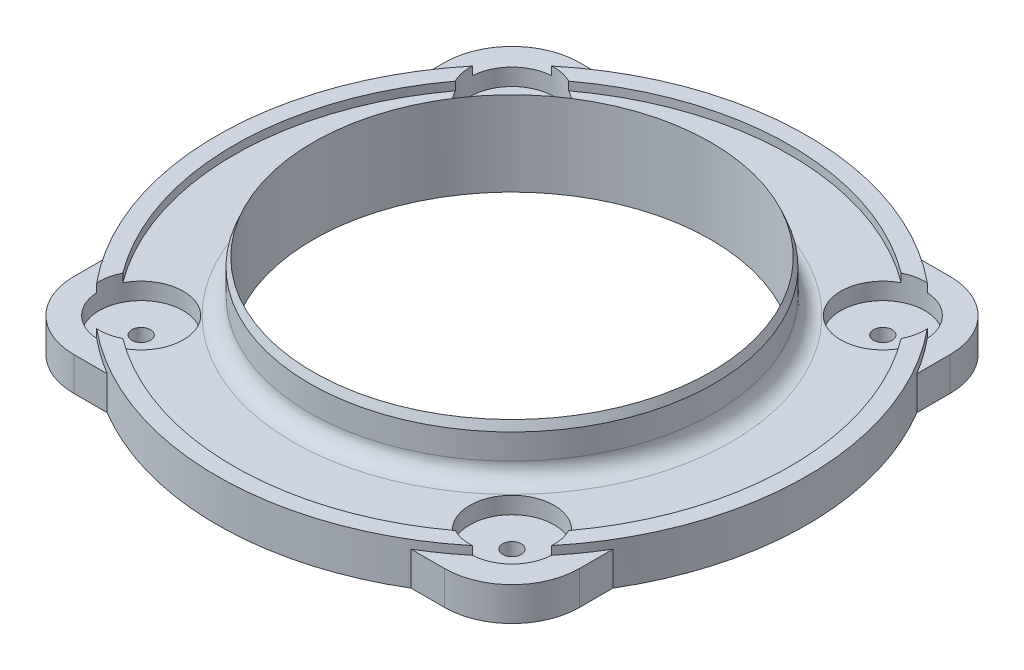
SolidWorks part; units mm, degrees
ref_plane "Front Plane" through (0, 0, 0) normal (0, 0, 1) x (1, 0, 0)
ref_plane "Top Plane" through (0, 0, 0) normal (0, 1, 0) x (1, 0, 0)
ref_plane "Right Plane" through (0, 0, 0) normal (1, 0, 0) x (0, 0, -1)
sketch "Sketch1" plane through (0, 0, 0) normal (0, 1, 0) x (1, 0, 0)
  line L1 (47.625, -47.625) -> (-47.625, -47.625)
  line L2 (47.625, -47.625) -> (47.625, 47.625)
  line L3 (47.625, 47.625) -> (-47.625, 47.625)
  line L4 (-47.625, -47.625) -> (-47.625, 47.625)
  line L5 (47.625, -47.625) -> (-47.625, 47.625) construction
  line L6 (47.625, 47.625) -> (-47.625, -47.625) construction
  circle A0 centre (0, 0) radius 37.465
  point P0 (0, 0)
  dimension "D1" = 74.93
  dimension "D3" = 95.25
extrude "Boss-Extrude1" add sketch "Sketch1" along normal blind 6.35
sketch "Sketch2" plane through (0, 6.35, 0) normal (0, 1, 0) x (1, 0, 0)
  line L1 (34.925, -34.925) -> (-34.925, -34.925) construction
  line L2 (34.925, -34.925) -> (34.925, 34.925) construction
  line L3 (34.925, 34.925) -> (-34.925, 34.925) construction
  line L4 (-34.925, -34.925) -> (-34.925, 34.925) construction
  line L5 (34.925, -34.925) -> (-34.925, 34.925) construction
  line L6 (34.925, 34.925) -> (-34.925, -34.925) construction
  circle A0 centre (-34.925, 34.925) radius 1.75
  point P0 (0, 0)
  dimension "D2" = 3.5
  dimension "D1" = 69.85
extrude "Cut-Extrude1" cut sketch "Sketch2" against normal through all
pattern_circular "CirPattern1" count 4 over 360 about axis through (0, 0, 0) along (0, 1, 0) of "Cut-Extrude1"
fillet "Fillet1" radius 12.7 4 edges at (-47.625, 3.175, -47.625) (-47.625, 3.175, 47.625) (47.625, 3.175, 47.625) (47.625, 3.175, -47.625)
sketch "Sketch4" plane through (0, 0, 0) normal (0, 0, 1) x (1, 0, 0)
  line L0 (-34.925, 6.35) -> (34.925, 6.35) construction
  line L1 (37.465, 6.35) -> (38.1, 6.35)
  line L2 (37.465, 6.35) -> (37.465, 12.7)
  line L3 (0, 0) -> (0, 34.8088) construction
  line L4 (37.465, 15.875) -> (38.1, 14.2875)
  line L5 (37.465, 12.7) -> (37.465, 15.875)
  line L6 (38.1, 14.2875) -> (38.1, 10.3505)
  line L11 (38.1, 6.35) -> (38.1, 10.3505)
  point P15 (38.1, 11.1125)
  dimension "D1" = 6.35
  dimension "D2" = 37.465
  dimension "D3" = 0.635
  dimension "D4" = 1.5875
  dimension "D5" = 4.7625
  dimension "D6" = 3.175
revolve "Revolve1" add sketch "Sketch4" angle 360 about L3
fillet "Fillet2" radius 3.175 1 edges at (0, 6.35, 38.1)
sketch "Sketch5" plane through (0, 6.35, 0) normal (0, 1, 0) x (1, 0, 0)
  circle A0 centre (0, 0) radius 52.3875 construction
  circle A1 centre (0, 0) radius 44.45
  circle A2 centre (0, 0) radius 55.5625
  circle A3 centre (-34.925, 34.925) radius 1.75
  circle A4 centre (-34.925, -34.925) radius 1.75
  circle A5 centre (34.925, -34.925) radius 1.75
  circle A6 centre (34.925, 34.925) radius 1.75
  circle A7 centre (-34.925, -34.925) radius 1.75 construction
  dimension "D1" = 104.775
  dimension "D2" = 88.9
  dimension "D3" = 3.175
extrude "Boss-Extrude2" add sketch "Sketch5" against normal through all contours A2 | A1 | A3 | A6 | A5 | A4
sketch "Sketch8" plane through (0, 6.35, 0) normal (0, 1, 0) x (1, 0, 0)
  circle A0 centre (0, 0) radius 52.3875
  circle A1 centre (0, 0) radius 55.5625
  arc A2 (-47.625, 28.6191) -> (-47.625, -28.6191) centre (0, 0) ccw construction
  dimension "D1" = 104.775
extrude "Boss-Extrude4" add sketch "Sketch8" along normal blind 1.5875
sketch "Sketch10" plane through (0, 6.35, 0) normal (0, 1, 0) x (1, 0, 0)
  circle A0 centre (-34.925, 34.925) radius 7.9375
  circle A1 centre (34.925, 34.925) radius 7.9375
  circle A2 centre (34.925, -34.925) radius 7.9375
  circle A3 centre (-34.925, -34.925) radius 7.9375
  dimension "D1" = 15.875
extrude "Cut-Extrude3" cut sketch "Sketch10" along normal through all and the other way blind 3.175
